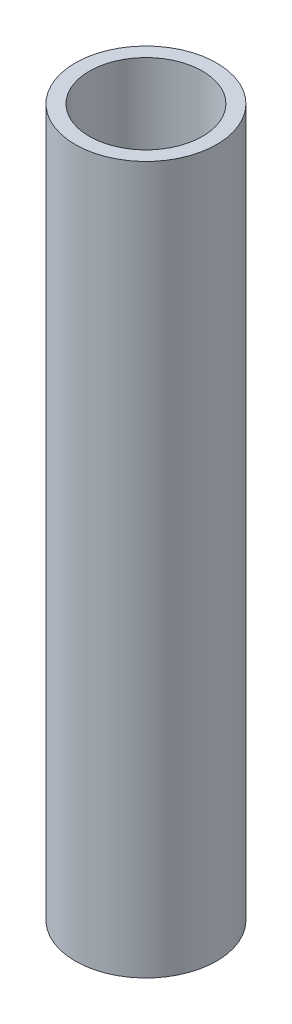
SolidWorks part; units mm, degrees
material "6061 Alloy"
ref_plane "Front Plane" through (0, 0, 0) normal (0, 0, 1) x (1, 0, 0)
ref_plane "Top Plane" through (0, 0, 0) normal (0, 1, 0) x (1, 0, 0)
ref_plane "Right Plane" through (0, 0, 0) normal (1, 0, 0) x (0, 0, -1)
sketch "Sketch1" plane through (0, 0, 0) normal (0, 1, 0) x (1, 0, 0)
  circle A0 centre (0, 0) radius 4
  circle A1 centre (0, 0) radius 5
  dimension "D1" = 8
  dimension "D2" = 10
extrude "Boss-Extrude1" add sketch "Sketch1" along normal mid plane 50
